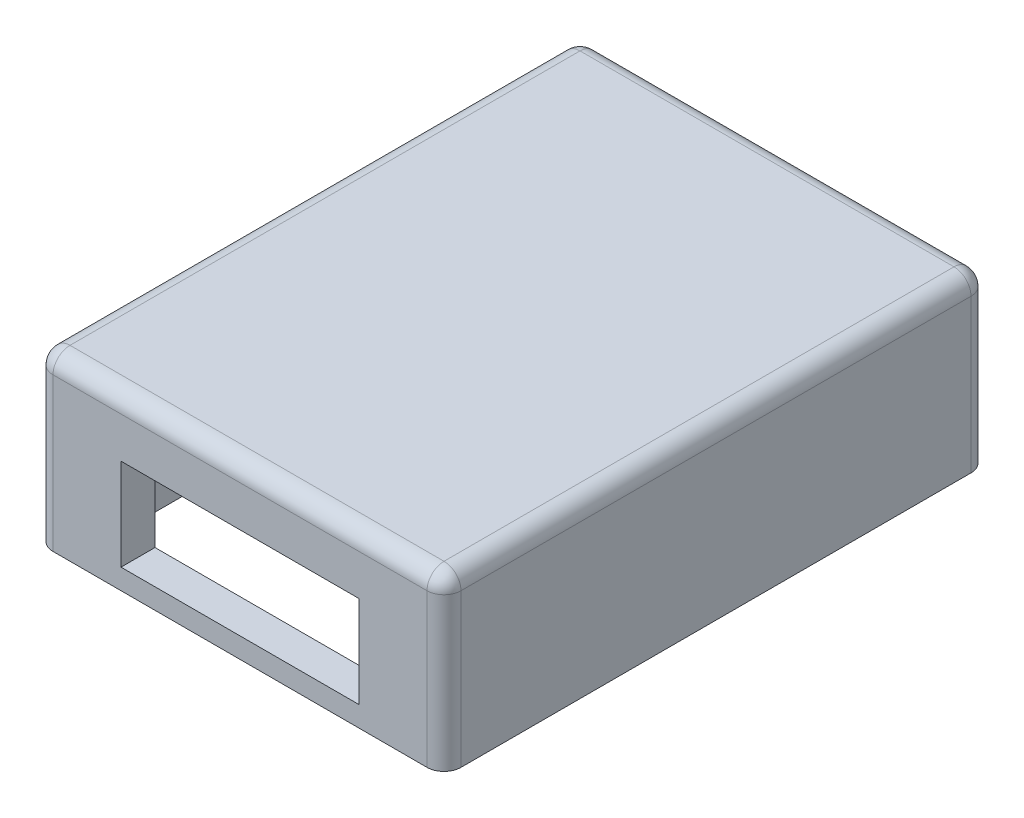
SolidWorks part; units mm, degrees
ref_plane "Front Plane" through (0, 0, 0) normal (0, 0, 1) x (1, 0, 0)
ref_plane "Top Plane" through (0, 0, 0) normal (0, 1, 0) x (1, 0, 0)
ref_plane "Right Plane" through (0, 0, 0) normal (1, 0, 0) x (0, 0, -1)
sketch "Sketch1" plane through (0, 0, 0) normal (0, 0, 1) x (1, 0, 0)
  line L1 (0, 0) -> (120, 0)
  line L2 (0, 0) -> (0, -50)
  line L3 (0, -50) -> (120, -50)
  line L4 (120, 0) -> (120, -50)
  dimension "D1" = 120
  dimension "D2" = 50
extrude "Boss-Extrude1" add sketch "Sketch1" along normal blind 160
fillet "Fillet1" radius 5 1 edges at (0, -25, 160)
fillet "Fillet2" radius 5 3 edges at (0, -25, 0) (120, -25, 0) (120, -25, 160)
sketch "Sketch2" plane through (0, -50, 0) normal (0, -1, 0) x (1, 0, 0)
  line L0 (5, 160) -> (115, 160) construction
  line L1 (10, 150) -> (110, 150)
  line L2 (10, 150) -> (10, 10)
  line L3 (10, 10) -> (110, 10)
  line L4 (110, 150) -> (110, 10)
  line L5 (120, 155) -> (120, 5) construction
  line L6 (5, 0) -> (115, 0) construction
  line L7 (0, 155) -> (0, 5) construction
  dimension "D1" = 10
  dimension "D2" = 10
  dimension "D3" = 10
  dimension "D4" = 10
extrude "Cut-Extrude1" cut sketch "Sketch2" against normal blind 45
fillet "Fillet3" radius 5 4 edges at (110, -27.5, 10) (10, -27.5, 10) (110, -27.5, 150) (10, -27.5, 150)
fillet "Fillet4" radius 5 8 edges at (11.4645, -5, 11.4645) (10, -5, 80) (11.4645, -5, 148.5355) (60, -5, 150) (108.5355, -5, 148.5355) (110, -5, 80) (108.5355, -5, 11.4645) (60, -5, 10)
fillet "Fillet5" radius 5 8 edges at (1.4645, 0, 158.5355) (60, 0, 160) (118.5355, 0, 158.5355) (120, 0, 80) (118.5355, 0, 1.4645) (60, 0, 0) (1.4645, 0, 1.4645) (0, 0, 80)
sketch "Sketch3" plane through (0, -50, 0) normal (0, -1, 0) x (1, 0, 0)
  circle A0 centre (5, 155) radius 1.5
  circle A1 centre (115, 155) radius 1.5
  circle A2 centre (115, 5) radius 1.5
  circle A3 centre (5, 5) radius 1.5
extrude "Cut-Extrude2" cut sketch "Sketch3" against normal blind 20
sketch "Sketch4" plane through (0, 0, 160) normal (0, 0, 1) x (1, 0, 0)
  line L0 (5, -50) -> (115, -50) construction
  line L1 (25, -17) -> (95, -17)
  line L2 (25, -17) -> (25, -44)
  line L3 (25, -44) -> (95, -44)
  line L4 (95, -17) -> (95, -44)
  line L7 (115, -50) -> (115, -5) construction
  dimension "D1" = 27
  dimension "D2" = 70
  dimension "D3" = 6
  dimension "D4" = 20
extrude "Cut-Extrude4" cut sketch "Sketch4" against normal blind 20
